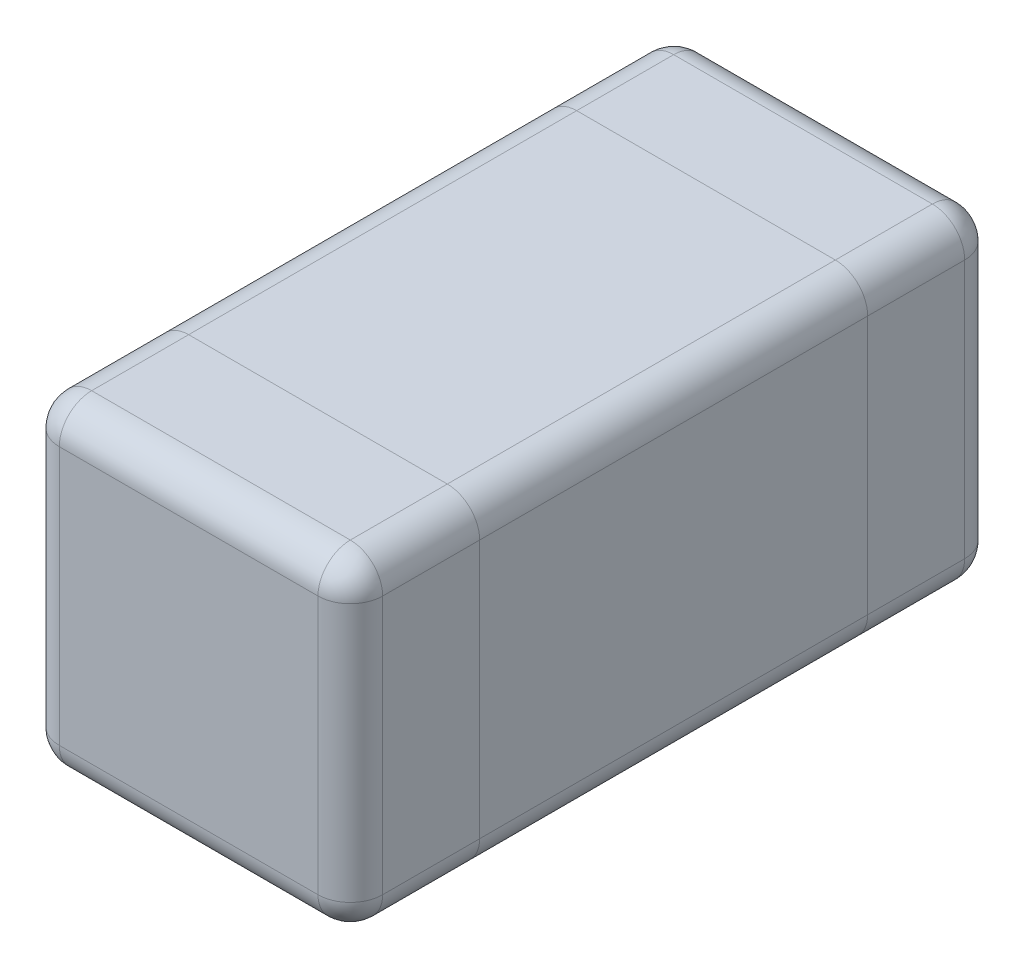
SolidWorks part; units mm, degrees
ref_plane "Front Plane" through (0, 0, 0) normal (0, 0, 1) x (1, 0, 0)
ref_plane "Top Plane" through (0, 0, 0) normal (0, 1, 0) x (1, 0, 0)
ref_plane "Right Plane" through (0, 0, 0) normal (1, 0, 0) x (0, 0, -1)
sketch "Sketch2" plane through (0, 0, 0) normal (0, 0, 1) x (1, 0, 0)
  line L1 (0, 0) -> (0.5, 0)
  line L2 (0, 0) -> (0, 0.5)
  line L3 (0, 0.5) -> (0.5, 0.5)
  line L4 (0.5, 0) -> (0.5, 0.5)
  dimension "D1" = 0.5
  dimension "D2" = 0.5
extrude "Boss-Extrude1" add sketch "Sketch2" along normal blind 0.2
sketch "Sketch3" plane through (0, 0, 0.2) normal (0, 0, 1) x (1, 0, 0)
  line L8 (0, 0.5) -> (0, 0)
  line L9 (0, 0) -> (0.5, 0)
  line L10 (0.5, 0) -> (0.5, 0.5)
  line L11 (0.5, 0.5) -> (0, 0.5)
  line L12 (0, 0.5) -> (0, 0)
  line L13 (0, 0) -> (0.5, 0)
  line L14 (0.5, 0) -> (0.5, 0.5)
  line L15 (0.5, 0.5) -> (0, 0.5)
  dimension "D1" = 0
extrude "Boss-Extrude2" add sketch "Sketch3" along normal blind 0.6 separate body contours L14 L15 L12 L13
sketch "Sketch5" plane through (0, 0, 0.8) normal (0, 0, 1) x (1, 0, 0)
  line L8 (0.5, 0) -> (0.5, 0.5)
  line L9 (0.5, 0.5) -> (0, 0.5)
  line L10 (0, 0.5) -> (0, 0)
  line L11 (0, 0) -> (0.5, 0)
  line L12 (0.5, 0) -> (0.5, 0.5)
  line L13 (0.5, 0.5) -> (0, 0.5)
  line L14 (0, 0.5) -> (0, 0)
  line L15 (0, 0) -> (0.5, 0)
  dimension "D1" = 0
extrude "Boss-Extrude4" add sketch "Sketch5" along normal blind 0.2 separate body contours L13 L14 L15 L12
fillet "Fillet2" radius 0.05 8 edges at (0, 0.25, 1) (0.25, 0, 1) (0.5, 0.25, 1) (0.25, 0.5, 1) (0, 0.5, 0.9) (0, 0, 0.9) (0.5, 0, 0.9) (0.5, 0.5, 0.9)
fillet "Fillet3" radius 0.05 4 edges at (0, 0, 0.5) (0.5, 0, 0.5) (0, 0.5, 0.5) (0.5, 0.5, 0.5)
fillet "Fillet4" radius 0.05 8 edges at (0, 0, 0.1) (0, 0.5, 0.1) (0.5, 0, 0.1) (0.5, 0.5, 0.1) (0.5, 0.25, 0) (0.25, 0, 0) (0, 0.25, 0) (0.25, 0.5, 0)
equation "\"cap_length\" = 0.2"
equation "\"length\" = 1.00 - \"cap_length\" * 2"
equation "\"D1@Boss-Extrude1\"= \"cap_length\""
equation "\"D1@Boss-Extrude4\"= \"cap_length\""
equation "\"D1@Boss-Extrude2\"= \"length\""
equation "\"height\" = 0.5"
equation "\"D1@Sketch2\" = \"width\""
equation "\"width\" = 0.5"
equation "\"D2@Sketch2\"= \"height\""
